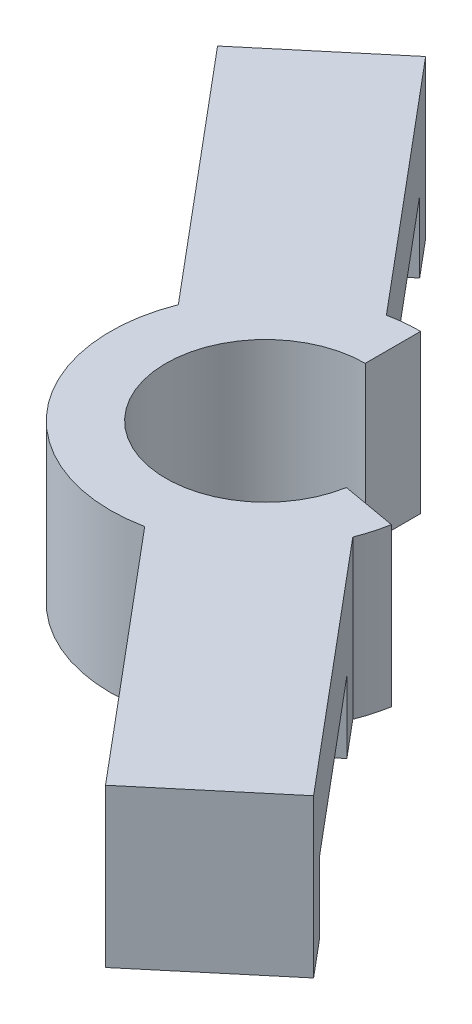
SolidWorks part; units mm, degrees
ref_plane "Front Plane" through (0, 0, 0) normal (0, 0, 1) x (1, 0, 0)
ref_plane "Top Plane" through (0, 0, 0) normal (0, 1, 0) x (1, 0, 0)
ref_plane "Right Plane" through (0, 0, 0) normal (1, 0, 0) x (0, 0, -1)
sketch "Sketch1" plane through (0, 0, 0) normal (0, 1, 0) x (1, 0, 0)
  line L0 (0, 5.4) -> (0, 8.4)
  line L1 (5.318, -0.9377) -> (8.2724, -1.4586)
  line L2 (-15.8213, 18.8551) -> (15.8213, -18.8551)
  line L3 (1.6838, -8.2295) -> (12.7571, -21.4262)
  line L4 (7.8121, -3.0872) -> (18.8854, -16.2839)
  line L5 (12.7571, -21.4262) -> (18.8854, -16.2839)
  line L7 (-7.8121, 3.0872) -> (-18.8854, 16.2839)
  line L8 (-18.8854, 16.2839) -> (-12.7571, 21.4262)
  line L9 (-1.6838, 8.2295) -> (-12.7571, 21.4262)
  line L11 (0, 0) -> (10.9987, 9.229) construction
  line L12 (-7.2204, 14.8279) -> (-13.3488, 9.6856) construction
  circle A0 centre (0, 0) radius 8.4
  circle A1 centre (0, 0) radius 5.4
  arc A3 (1.6838, -8.2295) -> (5.3994, -6.4348) centre (0, 0) cw
  arc A4 (-7.8121, 3.0872) -> (-5.3994, 6.4348) centre (0, 0) ccw
  point P11 (0, 0)
  point P13 (-5.3492, 0.0934)
  point P15 (-4.3493, 0.0759)
  point P18 (1.6838, -8.2295)
  point P19 (0, 0)
  point P26 (-0.0247, 0.0404)
  point P27 (0, 0)
  point P30 (0, 0)
  dimension "D1" = 3
  dimension "D3" = 16.8
  dimension "D6" = 10.8
  dimension "D5" = 16
  dimension "D2" = 100
  dimension "D4" = 8
extrude "Boss-Extrude2" add sketch "Sketch1" along normal blind 8.55
sketch "Sketch2" plane through (-3.0642, 0, 2.5712) normal (-0.766, 0, 0.6428) x (0.6428, 0, 0.766)
  line L0 (-16, 8.55) -> (-16, 0) construction
  line L1 (-7.3865, 8.55) -> (-24.6135, 8.55) construction
  line L2 (-7.3865, 0) -> (-24.6135, 0) construction
  line L3 (0, 0) -> (0, 8.55) construction
  line L4 (-7.3865, 0) -> (7.3865, 0) construction
  line L5 (7.3865, 8.55) -> (-7.3865, 8.55) construction
  line L6 (-22, 0) -> (-22, 3.8724)
  line L7 (-22, 3.8724) -> (-10, 3.8724)
  line L8 (-10, 3.8724) -> (-10, 0)
  line L9 (-10, 0) -> (-22, 0)
  line L11 (10, 3.8724) -> (10, 0)
  line L12 (22, 3.8724) -> (10, 3.8724)
  line L13 (22, 0) -> (22, 3.8724)
  line L14 (10, 0) -> (22, 0)
  line L15 (-16, 8.55) -> (-16, 0) construction
  dimension "D1" = 16
  dimension "D2" = 12
extrude "Cut-Extrude1" cut sketch "Sketch2" against normal blind 10
